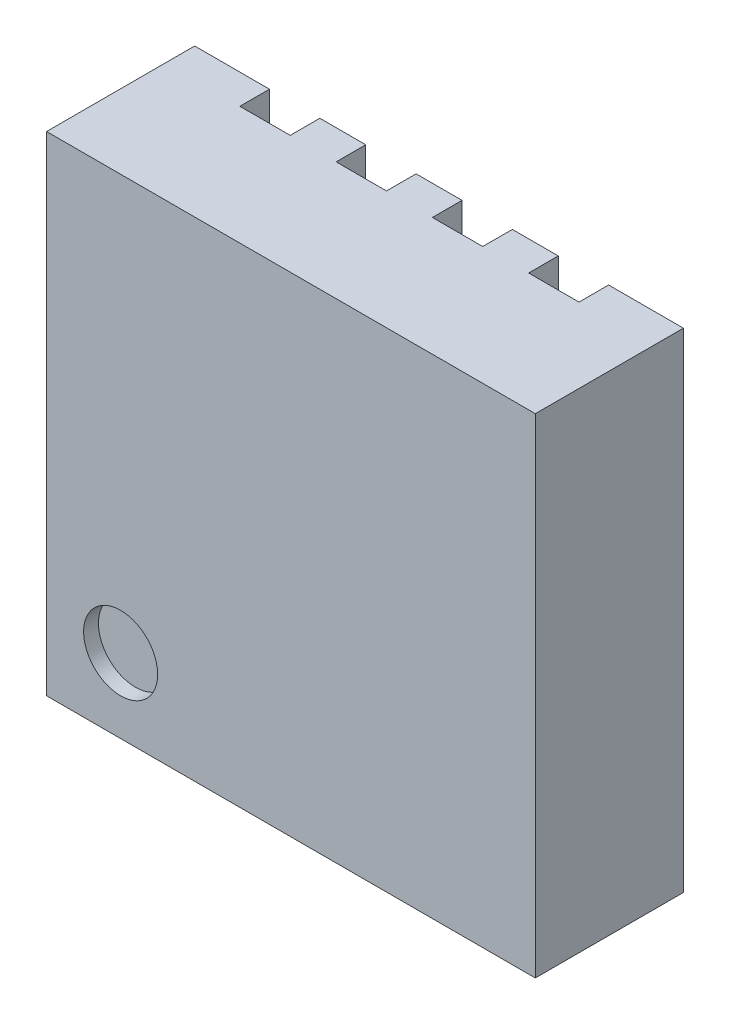
SolidWorks part; units mm, degrees
ref_plane "Спереди" through (0, 0, 0) normal (0, 0, 1) x (1, 0, 0)
ref_plane "Сверху" through (0, 0, 0) normal (0, 1, 0) x (1, 0, 0)
ref_plane "Справа" through (0, 0, 0) normal (1, 0, 0) x (0, 0, -1)
sketch "Эскиз1" plane through (0, 0, 0) normal (0, 0, 1) x (1, 0, 0)
  line L1 (-1.65, 1.65) -> (1.65, 1.65)
  line L2 (-1.65, 1.65) -> (-1.65, -1.65)
  line L3 (-1.65, -1.65) -> (1.65, -1.65)
  line L4 (1.65, 1.65) -> (1.65, -1.65)
  line L5 (-1.65, 1.65) -> (1.65, -1.65) construction
  line L6 (-1.65, -1.65) -> (1.65, 1.65) construction
  point P0 (0, 0)
  dimension "D1" = 3.3
  dimension "D2" = 3.3
extrude "Бобышка-Вытянуть1" add sketch "Эскиз1" along normal blind 1
sketch "Эскиз2" plane through (0, 0, 1) normal (0, 0, 1) x (1, 0, 0)
  line L0 (-1.65, -1.65) -> (1.65, -1.65) construction
  line L1 (-1.65, 1.65) -> (-1.65, -1.65) construction
  circle A0 centre (-1.15, -1.15) radius 0.25
  dimension "D1" = 0.5
  dimension "D2" = 0.5
extrude "Вырез-Вытянуть1" cut sketch "Эскиз2" against normal blind 0.1
sketch "Эскиз3" plane through (0, 0, 0) normal (0, 0, -1) x (-1, 0, 0)
  line L0 (-1.145, 1.65) -> (-1.145, -0.46)
  line L1 (-1.145, -0.46) -> (1.145, -0.46)
  line L2 (1.145, -0.46) -> (1.145, 1.65)
  line L3 (1.145, 1.65) -> (0.805, 1.65)
  line L4 (0.805, 1.65) -> (0.805, 1.25)
  line L5 (0.805, 1.25) -> (0.495, 1.25)
  line L6 (0.495, 1.25) -> (0.495, 1.65)
  line L7 (-0.495, 1.65) -> (-0.495, 1.25)
  line L8 (-0.495, 1.25) -> (-0.805, 1.25)
  line L9 (-0.805, 1.25) -> (-0.805, 1.65)
  line L10 (-0.805, 1.65) -> (-1.145, 1.65)
  line L11 (-0.495, 1.65) -> (-0.155, 1.65)
  line L12 (-0.155, 1.65) -> (-0.155, 1.25)
  line L13 (-0.155, 1.25) -> (0.155, 1.25)
  line L14 (0.155, 1.25) -> (0.155, 1.65)
  line L15 (0.155, 1.65) -> (0.495, 1.65)
  line L16 (1.145, -1.65) -> (1.145, -1.05)
  line L17 (1.145, -1.05) -> (-0.495, -1.05)
  line L18 (-0.495, -1.05) -> (-0.495, -1.65)
  line L19 (-0.495, -1.65) -> (-0.155, -1.65)
  line L20 (-0.155, -1.65) -> (-0.155, -1.45)
  line L21 (-0.155, -1.45) -> (0.155, -1.45)
  line L22 (0.155, -1.45) -> (0.155, -1.65)
  line L23 (0.155, -1.65) -> (0.495, -1.65)
  line L24 (0.495, -1.65) -> (0.495, -1.45)
  line L25 (0.495, -1.45) -> (0.805, -1.45)
  line L26 (0.805, -1.45) -> (0.805, -1.65)
  line L27 (0.805, -1.65) -> (1.145, -1.65)
  line L28 (-0.805, -1.65) -> (-0.805, -1.15)
  line L29 (-0.805, -1.15) -> (-1.145, -1.15)
  line L30 (-1.145, -1.15) -> (-1.145, -1.65)
  line L31 (-1.145, -1.65) -> (-0.805, -1.65)
  line L32 (-1.65, 1.65) -> (1.65, 1.65) construction
  line L33 (1.65, -1.65) -> (-1.65, -1.65) construction
  dimension "D1" = 2.29
  dimension "D2" = 1.71
  dimension "D3" = 0.31
  dimension "D4" = 0.31
  dimension "D5" = 0.31
  dimension "D6" = 0.6
  dimension "D7" = 0.5
  dimension "D8" = 0.34
  dimension "D9" = 0.4
  dimension "D10" = 0.2
  dimension "D11" = 1.145
extrude "Вырез-Вытянуть2" cut sketch "Эскиз3" against normal blind 0.2
